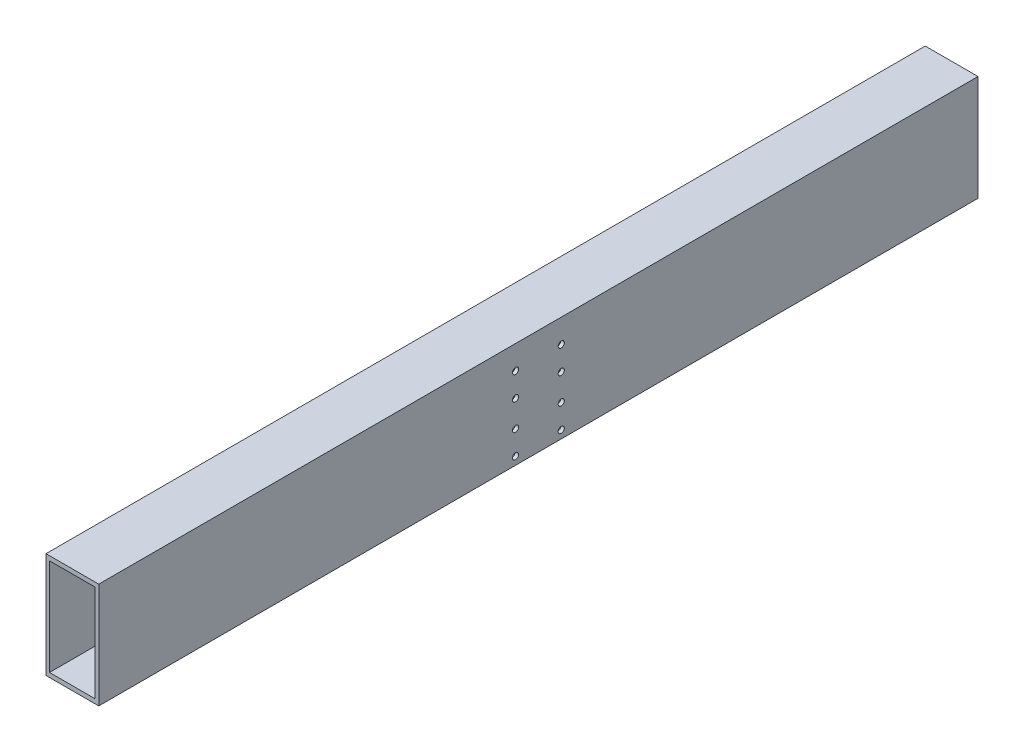
SolidWorks part; units mm, degrees
material "1.0037 (S235JR)"
ref_plane "Front Plane" through (0, 0, 0) normal (0, 0, 1) x (1, 0, 0)
ref_plane "Top Plane" through (0, 0, 0) normal (0, 1, 0) x (1, 0, 0)
ref_plane "Right Plane" through (0, 0, 0) normal (1, 0, 0) x (0, 0, -1)
curve "Curve1"
  spline degree 1 poles (0, 0, -500) (0, 0, 500) knots 0 0 1 1
sketch "Sketch1" plane through (0, 0, 0) normal (0, 0, 1) x (1, 0, 0)
  line L0 (0, 35.3535) -> (0, -33.8384) construction
  line L1 (-30, 60) -> (30, 60)
  line L2 (-30, 60) -> (-30, -60)
  line L3 (-30, -60) -> (30, -60)
  line L4 (30, 60) -> (30, -60)
  line L5 (-26, 55) -> (26, 55)
  line L6 (-26, 55) -> (-26, -55)
  line L7 (-26, -55) -> (26, -55)
  line L8 (26, 55) -> (26, -55)
  line L9 (-39.3939, 0) -> (41.5152, 0) construction
  dimension "D1" = 60
  dimension "D2" = 52
  dimension "D3" = 120
  dimension "D4" = 110
sweep "Sweep1" add profiles "Sketch1" path "Curve1"
sketch "Sketch2" plane through (30, 0, 0) normal (1, 0, 0) x (0, 0, -1)
  line L0 (26, 88.4507) -> (26, -117.3154) construction
  line L1 (-500, 60) -> (500, 60) construction
  point P3 (26, 33)
  point P4 (26, 6)
  point P5 (26, -24)
  point P6 (26, -51)
  dimension "D1" = 27
  dimension "D2" = 27
  dimension "D3" = 30
  dimension "D4" = 27
  dimension "D5" = 26
hole_wizard "Ø7.0 (7) Diameter Hole1" positions "Sketch3" profile "Sketch5" hole size "Ø7.0" standard "ISO" end condition through all
sketch "Sketch3" plane through (30, 0, 0) normal (1, 0, 0) x (0, 0, -1)
  point P0 (26, 33)
  point P3 (26, 6)
  point P6 (26, -24)
  point P9 (26, -51)
sketch "Sketch5" plane through (30, 33, -26) normal (0, 1, 0) x (0, 0, -1)
  line L0 (0, 0) -> (0, 60)
  line L1 (0, 60) -> (3.5, 60)
  line L2 (3.5, 60) -> (3.5, 0)
  line L5 (3.5, 0) -> (0, 0)
  line L11 (0, -6.35) -> (0, 107.95) construction
  dimension "Thru Hole Dia." = 7
  dimension "Thru Hole Depth" = 60
mirror "Mirror1" about plane through (0, 0, 0) normal (0, 0, 1) of "Ø7.0 (7) Diameter Hole1"
